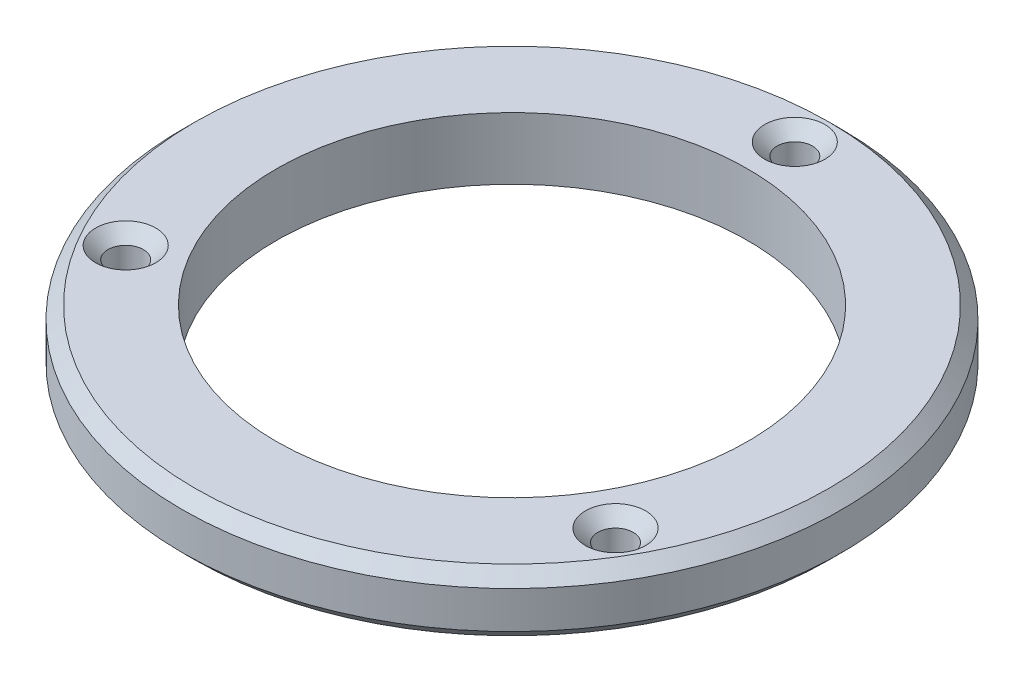
SolidWorks part; units mm, degrees
ref_plane "Front Plane" through (0, 0, 0) normal (0, 0, 1) x (1, 0, 0)
ref_plane "Top Plane" through (0, 0, 0) normal (0, 1, 0) x (1, 0, 0)
ref_plane "Right Plane" through (0, 0, 0) normal (1, 0, 0) x (0, 0, -1)
sketch "Sketch1" plane through (0, 0, 0) normal (0, 1, 0) x (1, 0, 0)
  circle A0 centre (0, 0) radius 26.543
  circle A1 centre (0, 0) radius 19
  circle A2 centre (0, 22.7767) radius 1.425
  circle A3 centre (19.7252, -11.3884) radius 1.425
  circle A4 centre (-19.7252, -11.3884) radius 1.425
  point P12 (0, 0)
  dimension "D1" = 3
  dimension "D2" = 38
extrude "Boss-Extrude1" add sketch "Sketch1" along normal blind 5
chamfer "Chamfer1" distance 1 angle 45 1 edges at (0, 5, -21.3517)
chamfer "Chamfer2" distance 1 angle 45 1 edges at (-19.7252, 5, 12.8134)
chamfer "Chamfer3" distance 1 angle 45 1 edges at (19.7252, 5, 12.8134)
chamfer "Chamfer4" distance 1 angle 45 1 edges at (0, 5, 26.543)
chamfer "Chamfer5" distance 1 angle 45 1 edges at (0, 0, 26.543)
